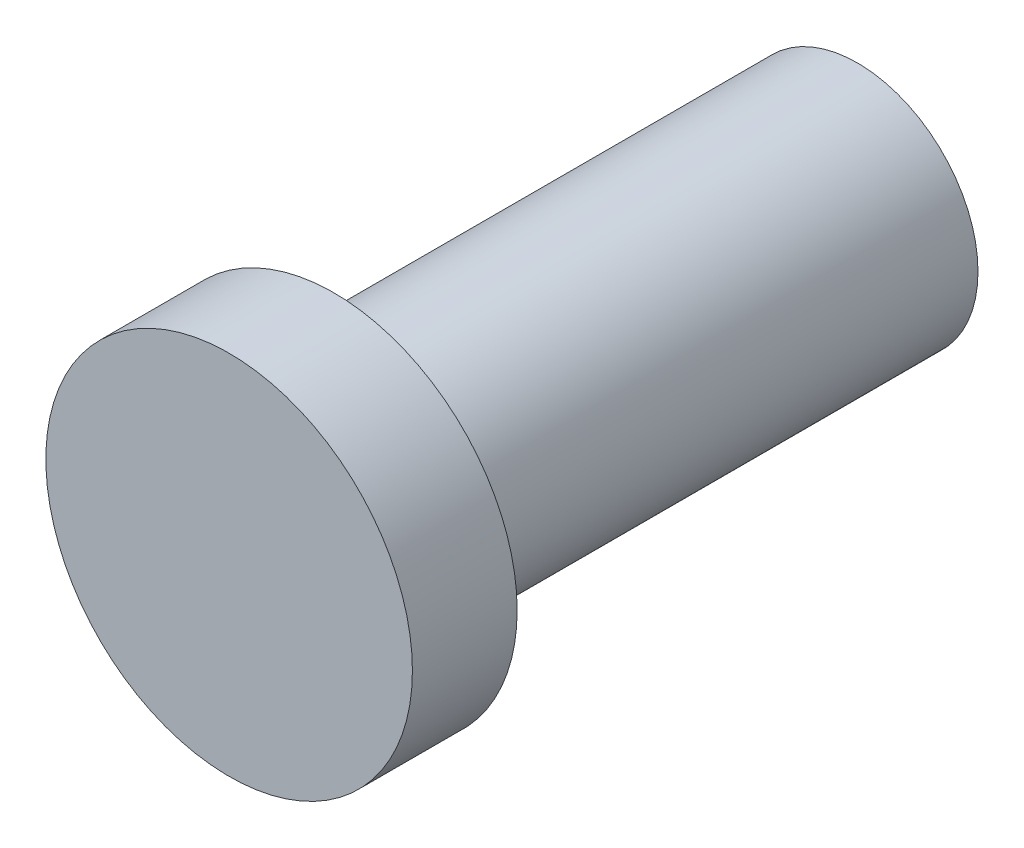
SolidWorks part; units mm, degrees
ref_plane "Front" through (0, 0, 0) normal (0, 0, 1) x (1, 0, 0)
ref_plane "Top" through (0, 0, 0) normal (0, 1, 0) x (1, 0, 0)
ref_plane "Right" through (0, 0, 0) normal (1, 0, 0) x (0, 0, -1)
sketch "草图1" plane through (0, 0, 0) normal (0, 0, 1) x (1, 0, 0)
  circle A0 centre (0, 0) radius 1.15
  dimension "D1" = 2.3
extrude "凸台-拉伸1" add sketch "草图1" along normal blind 5
sketch "草图2" plane through (0, 0, 5) normal (0, 0, 1) x (1, 0, 0)
  circle A0 centre (0, 0) radius 1.75
  dimension "D1" = 3.5
extrude "凸台-拉伸2" add sketch "草图2" along normal blind 1
